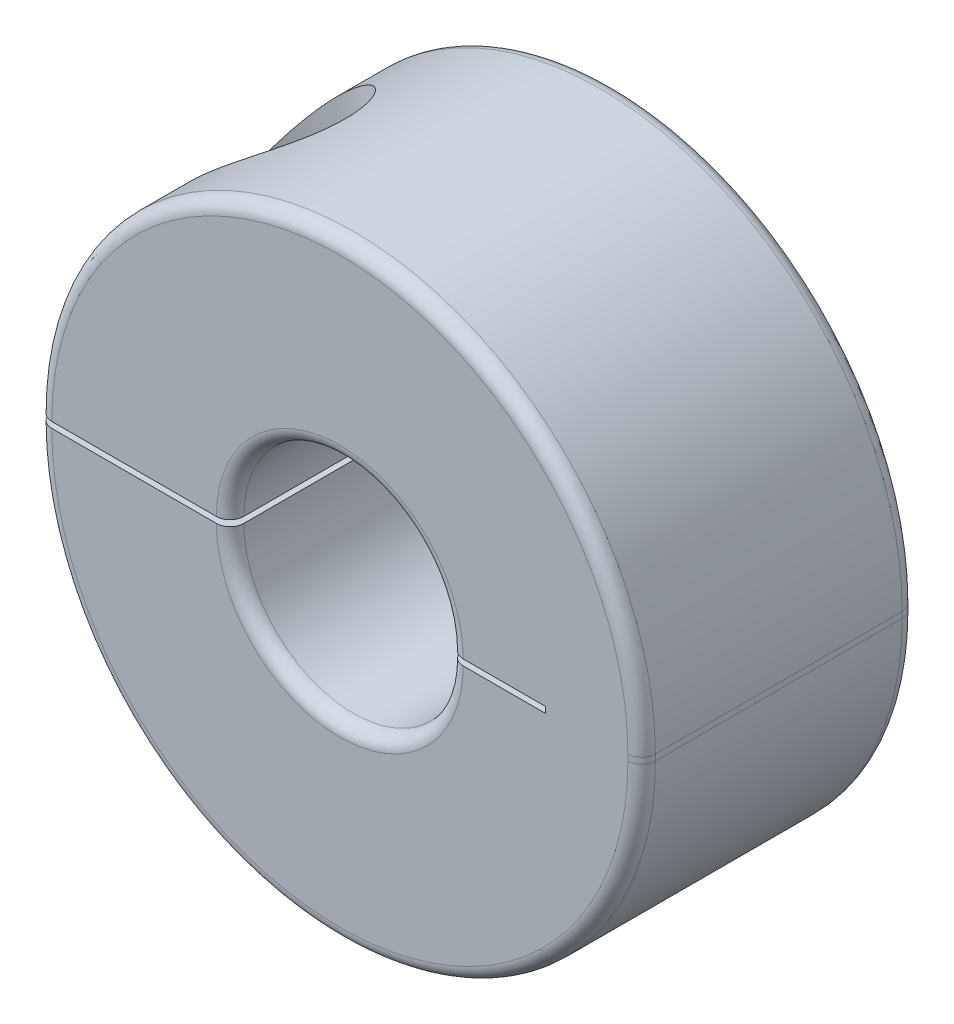
SolidWorks part; units mm, degrees
material "Alloy Steel"
ref_plane "Front Plane" through (0, 0, 0) normal (0, 0, 1) x (1, 0, 0)
ref_plane "Top Plane" through (0, 0, 0) normal (0, 1, 0) x (1, 0, 0)
ref_plane "Right Plane" through (0, 0, 0) normal (1, 0, 0) x (0, 0, -1)
sketch "Sketch1" plane through (0, 0, 0) normal (0, 0, 1) x (1, 0, 0)
  line L0 (-8.7312, 0) -> (-3.175, 0) construction
  line L1 (-8.7313, 0.0873) -> (-3.175, 0.0873)
  line L2 (-8.7313, -0.0873) -> (-3.175, -0.0873)
  line L3 (3.175, 0.0873) -> (8.7313, 0.0873) construction
  line L4 (3.175, -0.0873) -> (8.7313, -0.0873) construction
  line L5 (0, 0) -> (0, 8.7313) construction
  line L6 (8.7313, 0.0873) -> (8.7313, -0.0873)
  line L7 (3.175, 0.0873) -> (5.9531, 0.0873)
  line L8 (5.9531, 0.0873) -> (5.9531, -0.0873)
  line L10 (5.9531, -0.0873) -> (3.175, -0.0873)
  circle A0 centre (0, 0) radius 8.7313 construction
  circle A1 centre (0, 0) radius 3.175 construction
  arc A2 (-8.7313, 0.0873) -> (8.7313, 0.0873) centre (0, 0.0873) cw
  arc A3 (-8.7313, -0.0873) -> (8.7313, -0.0873) centre (0, -0.0873) ccw
  arc A4 (-3.175, 0.0873) -> (3.175, 0.0873) centre (0, 0.0873) cw
  arc A5 (-3.175, -0.0873) -> (3.175, -0.0873) centre (0, -0.0873) ccw
  point P4 (8.7312, 0)
  dimension "Bore Dia" = 6.35
  dimension "OD" = 17.4625
  dimension "Separation" = 0.1746
extrude "Extrude1" add sketch "Sketch1" along normal mid plane 7.9375
sketch "Sketch4" plane through (0, 0, 0) normal (0, 0, 1) x (1, 0, 0)
  line L0 (-5.9531, 8.8186) -> (-3.8195, 8.8186)
  line L1 (-3.8195, 8.8186) -> (-3.8195, 0.7985)
  line L2 (-3.8195, 0.7985) -> (-4.5307, 0.7985)
  line L3 (-4.5307, 0.7985) -> (-4.5307, -8.8186)
  line L4 (-4.5307, -8.8186) -> (-5.9531, -8.8186)
  line L5 (-5.9531, -8.8186) -> (-5.9531, 8.8186)
  line L6 (-3.8195, 3.6433) -> (-8.0867, 3.6433) construction
  line L7 (-5.9531, 8.8186) -> (-5.9531, 11.3586) construction
  line L8 (-3.8195, 8.8186) -> (0, 8.8186) construction
  line L9 (0, -8.8186) -> (-4.5307, -8.8186) construction
  line L10 (-8.7313, 0) -> (-3.175, 0) construction
  line L11 (-8.7313, 0.0873) -> (-3.175, 0.0873) construction
  circle A0 centre (0, 0) radius 8.7313 construction
  arc A1 (8.7313, 0.0873) -> (-8.7313, 0.0873) centre (0, 0.0873) ccw construction
  circle A2 centre (0, 0) radius 3.175 construction
  arc A3 (-8.7313, -0.0873) -> (8.7313, -0.0873) centre (0, -0.0873) ccw construction
  point P13 (-5.9531, 0)
  point P19 (-5.9531, 0)
  point P20 (-5.9531, 3.6433)
  dimension "D1" = 2.8448
  dimension "D2" = 5.5563
  dimension "D3" = 0.7112
  dimension "D4" = 4.2672
  dimension "D5" = 2.54
  dimension "Screw Dia" = 2.8448
revolve "Cut-Revolve1" cut sketch "Sketch4" angle 360 about L5
sketch "Sketch6" plane through (0, 0, 0) normal (0, 0, 1) x (1, 0, 0)
  line L0 (-5.9531, 3.6433) -> (-3.8195, 3.6433)
  line L1 (-3.8195, 3.6433) -> (-8.0867, 3.6433) construction
  line L2 (-3.8195, 3.6433) -> (-3.8195, 0.7985)
  line L3 (-3.8195, 0.7985) -> (-4.5307, 0.7985)
  line L4 (-4.5307, 0.7985) -> (-4.5307, -4.8911)
  line L5 (-4.5307, 0.7985) -> (-4.5307, -8.8186) construction
  line L6 (-4.5307, -4.8911) -> (-5.9531, -4.8911)
  line L7 (-5.9531, -8.8186) -> (-5.9531, 8.8186) construction
  line L8 (-5.9531, -4.8911) -> (-5.9531, 3.6433)
  line L9 (-4.5307, -4.8911) -> (-7.3755, -4.8911) construction
  dimension "Head Ht" = 2.8448
  dimension "Screw Lg" = 8.5344
revolve "Revolve1" add sketch "Sketch6" angle 360 about L8
sketch "Sketch7" plane through (0, 3.6433, 0) normal (0, 1, 0) x (-1, 0, 0)
  line L1 (5.9531, -1.314) -> (7.091, -0.657)
  line L2 (7.091, -0.657) -> (7.091, 0.657)
  line L3 (7.091, 0.657) -> (5.9531, 1.314)
  line L4 (5.9531, 1.314) -> (4.8152, 0.657)
  line L5 (4.8152, 0.657) -> (4.8152, -0.657)
  line L6 (4.8152, -0.657) -> (5.9531, -1.314)
  circle A0 centre (5.9531, 0) radius 1.1379 construction
  dimension "D1" = 2.2758
extrude "Cut-Extrude2" cut sketch "Sketch7" against normal blind 1.4224
fillet "Fillet1" radius 0.3969 8 edges at (0, 3.2623, -3.9688) (0, 3.2623, 3.9688) (0, 8.8186, -3.9688) (0, 8.8186, 3.9688) (0, -8.8186, -3.9688) (0, -8.8186, 3.9688) (8.7313, 0, -3.9688) (8.7313, 0, 3.9688)
fillet "Fillet2" radius 0.3969 2 edges at (0, -3.2623, -3.9688) (0, -3.2623, 3.9688)
chamfer "Chamfer2" distance 0.254 angle 45 1 edges at (-5.9531, 3.6433, -2.1336)
equation "\"D1@Sketch4\" = \"Screw Dia@Sketch4\""
equation "\"D4@Sketch4\" = \"Screw Dia@Sketch4\"*1.5"
equation "\"D1@Sketch7\" = \"Screw Dia@Sketch4\"*.8"
equation "\"D1@Cut-Extrude2\" = \"Head Ht@Sketch6\"/2"
equation "\"D3@Sketch4\" = \"D1@Sketch4\"*.25"
equation "\"D1@Fillet1\" = \"Width@Extrude1\"*.05"
equation "\"D1@Fillet2\" = \"D1@Fillet1\""
equation "\"Screw Lg@Sketch6\" = \"Head Ht@Sketch6\"*3"
equation "\"Separation@Sketch1\" = \"OD@Sketch1\"*.01"
